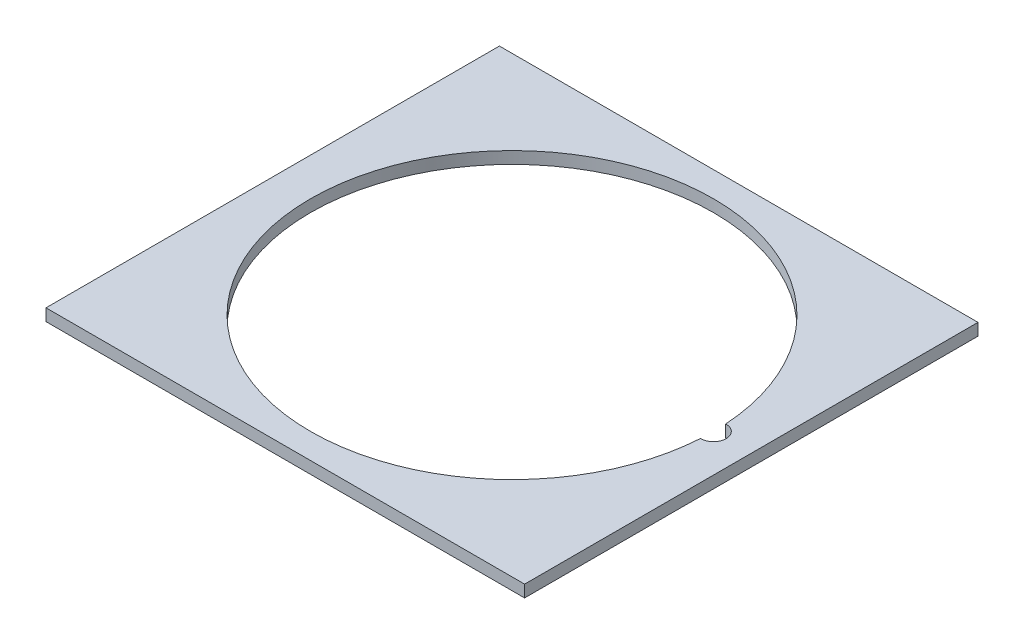
SolidWorks part; units mm, degrees
ref_plane "Front Plane" through (0, 0, 0) normal (0, 0, 1) x (1, 0, 0)
ref_plane "Top Plane" through (0, 0, 0) normal (0, 1, 0) x (1, 0, 0)
ref_plane "Right Plane" through (0, 0, 0) normal (1, 0, 0) x (0, 0, -1)
sketch "Sketch1" plane through (0, 0, 0) normal (0, 1, 0) x (1, 0, 0)
  line L0 (-95, -90) -> (95, 90) construction
  line L1 (-95, 90) -> (95, 90)
  line L2 (-95, 90) -> (-95, -90)
  line L3 (-95, -90) -> (95, -90)
  line L4 (95, 90) -> (95, -90)
  arc A0 (79.8438, 4.9976) -> (79.8438, -4.9976) centre (0, 0) ccw
  arc A1 (79.8438, -4.9976) -> (79.8438, 4.9976) centre (80, 0) ccw
  dimension "D1" = 160
  dimension "D2" = 5
  dimension "D3" = 190
  dimension "D4" = 180
extrude "Boss-Extrude1" add sketch "Sketch1" along normal blind 4.7625
